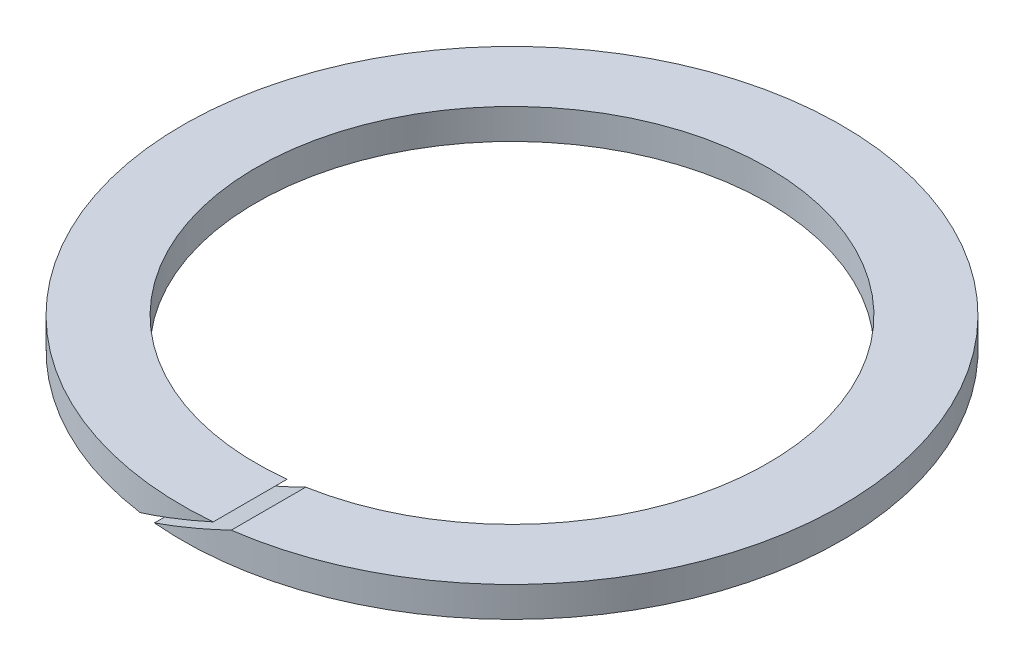
SolidWorks part; units mm, degrees
ref_plane "Front Plane" through (0, 0, 0) normal (0, 0, 1) x (1, 0, 0)
ref_plane "Top Plane" through (0, 0, 0) normal (0, 1, 0) x (1, 0, 0)
ref_plane "Right Plane" through (0, 0, 0) normal (1, 0, 0) x (0, 0, -1)
sketch "Sketch1" plane through (0, 0, 0) normal (0, 1, 0) x (1, 0, 0)
  line L0 (0, -10.5156) -> (0, -13.5382) construction
  circle A0 centre (0, 0) radius 10.5156 construction
  circle A1 centre (0, 0) radius 13.5382 construction
  dimension "ID" = 21.0312
  dimension "OD" = 27.0764
  dimension "Width" = 3.0226
sketch "Sketch2" plane through (0, 0, 0) normal (1, 0, 0) x (0, 0, -1)
  line L0 (0, 0.6223) -> (0, -0.6223) construction
  line L2 (13.5382, 0) -> (-13.5382, 0) construction
  point P5 (0, 0)
  dimension "Thickness" = 1.2446
sketch "Sketch3" plane through (0, 0, 0) normal (0, 1, 0) x (1, 0, 0)
  circle A0 centre (0, 0) radius 13.5382 construction
  circle A1 centre (0, 0) radius 13.5382
  circle A2 centre (0, 0) radius 10.5156 construction
  circle A3 centre (0, 0) radius 10.5156
extrude "Boss-Extrude1" add sketch "Sketch3" against normal up to vertex (0.6223 mm away) and the other way up to vertex (0.6223 mm away) up to point (0, -0.6223, 0) other way up to point (0, 0.6223, 0)
sketch "Sketch4" plane through (0, 0, 0) normal (0, 0, 1) x (1, 0, 0)
  line L0 (2.8849, 1.1656) -> (-2.8849, -1.1656) construction
  line L1 (13.5382, 0) -> (-13.5382, 0) construction
  line L2 (2.8383, 1.281) -> (-2.9316, -1.0502)
  line L3 (2.9316, 1.0502) -> (-2.8383, -1.281)
  line L4 (2.8383, 1.281) -> (2.9316, 1.0502)
  line L5 (-2.9316, -1.0502) -> (-2.8383, -1.281)
  dimension "D1" = 22
  dimension "D4" = 6.223
  dimension "D2" = 0.1245
  dimension "D3" = 0.1245
extrude "Cut-Extrude1" cut sketch "Sketch4" along normal through all
equation "\"D3@Sketch4\"=\"D2@Sketch4\""
equation "\"D2@Sketch4\"=\"Thickness@Sketch2\"/10"
equation "\"D4@Sketch4\"=\"Thickness@Sketch2\"*5"
